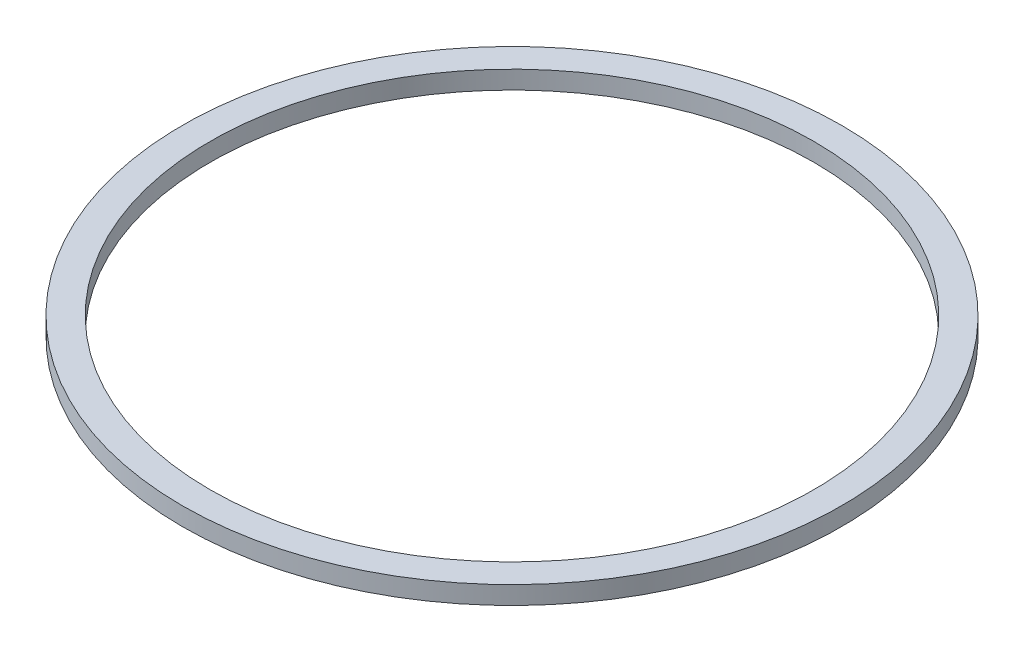
SolidWorks part; units mm, degrees
material "Silicon"
ref_plane "Front Plane" through (0, 0, 0) normal (0, 0, 1) x (1, 0, 0)
ref_plane "Top Plane" through (0, 0, 0) normal (0, 1, 0) x (1, 0, 0)
ref_plane "Right Plane" through (0, 0, 0) normal (1, 0, 0) x (0, 0, -1)
sketch "Sketch1" plane through (0, 0, 0) normal (0, 1, 0) x (1, 0, 0)
  circle A0 centre (0, 0) radius 25
  circle A1 centre (0, 0) radius 27.3
  dimension "D1" = 50
  dimension "D2" = 54.6
extrude "Boss-Extrude1" add sketch "Sketch1" along normal blind 1.5
